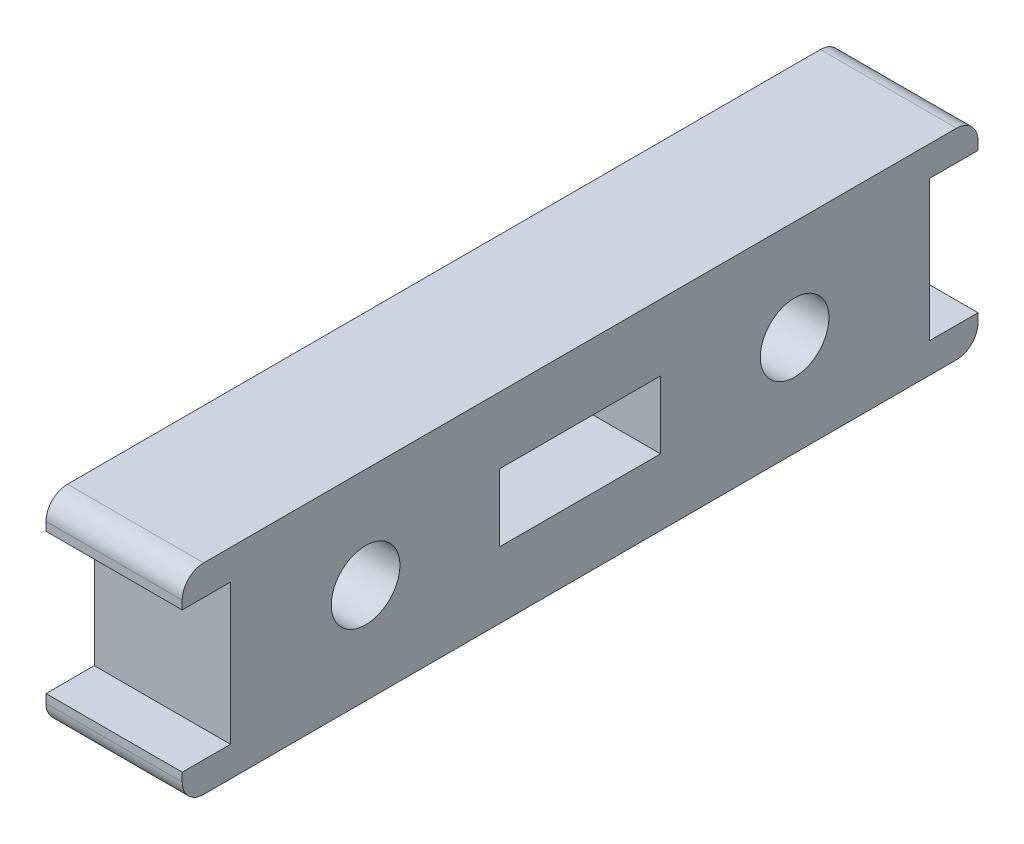
SolidWorks part; units mm, degrees
ref_plane "Front" through (0, 0, 0) normal (0, 0, 1) x (1, 0, 0)
ref_plane "Top" through (0, 0, 0) normal (0, 1, 0) x (1, 0, 0)
ref_plane "Right" through (0, 0, 0) normal (1, 0, 0) x (0, 0, -1)
ref_plane "Plane1" through (6.35, 0, 0) normal (1, 0, 0) x (0, 0, -1)
sketch "Sketch1" plane through (6.35, 0, 0) normal (1, 0, 0) x (0, 0, -1)
  line L0 (37.1, -7.95) -> (34.85, -7.95)
  line L1 (34.85, -7.95) -> (34.85, -1.4)
  line L2 (34.85, -1.4) -> (37.1, -1.4)
  line L3 (37.1, -1.4) -> (37.1, 0)
  line L4 (37.1, 0) -> (0, 0)
  line L5 (0, 0) -> (0, -1.4)
  line L6 (0, -1.4) -> (2.25, -1.4)
  line L7 (2.25, -1.4) -> (2.25, -7.95)
  line L8 (2.25, -7.95) -> (0, -7.95)
  line L9 (0, -7.95) -> (0, -9.35)
  line L10 (0, -9.35) -> (37.1, -9.35)
  line L11 (37.1, -9.35) -> (37.1, -7.95)
extrude "Boss-Extrude1" add sketch "Sketch1" against normal blind 6.35
fillet "Fillet1" radius 1 4 edges at (3.175, 0, -37.1) (3.175, 0, 0) (3.175, -9.35, 0) (3.175, -9.35, -37.1)
sketch "Sketch2" plane through (0, 0, 0) normal (-1, 0, 0) x (0, 0, 1)
  line L0 (-14.8, -3.1) -> (-22.3, -3.1)
  line L1 (-22.3, -3.1) -> (-22.3, -6.25)
  line L2 (-22.3, -6.25) -> (-14.8, -6.25)
  line L3 (-14.8, -6.25) -> (-14.8, -3.1)
extrude "Cut-Extrude1" cut sketch "Sketch2" against normal through all
hole_wizard "Ø3.2 (3.2) Diameter Hole1" positions "Sketch4" profile "Sketch3" hole size "Ø3.2" standard "ANSI Metric"
sketch "Sketch4" plane through (6.35, 0, 0) normal (1, 0, 0) x (0, 0, -1)
  point P0 (28.55, -4.675)
sketch "Sketch3" plane through (6.35, -4.675, -28.55) normal (0, 1, 0) x (0, 0, -1)
  line L0 (0, 0) -> (0, 6.35)
  line L1 (0, 6.35) -> (1.6, 6.35)
  line L2 (1.6, 6.35) -> (1.6, 0)
  line L5 (1.6, 0) -> (0, 0)
  line L11 (0, -6.35) -> (0, 107.95) construction
  dimension "Thru Hole Dia." = 3.2
  dimension "Thru Hole Depth" = 6.35
hole_wizard "Ø3.2 (3.2) Diameter Hole2" positions "Sketch6" profile "Sketch5" hole size "Ø3.2" standard "ANSI Metric"
sketch "Sketch6" plane through (6.35, 0, 0) normal (1, 0, 0) x (0, 0, -1)
  point P0 (8.55, -4.675)
sketch "Sketch5" plane through (6.35, -4.675, -8.55) normal (0, 1, 0) x (0, 0, -1)
  line L0 (0, 0) -> (0, 6.35)
  line L1 (0, 6.35) -> (1.6, 6.35)
  line L2 (1.6, 6.35) -> (1.6, 0)
  line L5 (1.6, 0) -> (0, 0)
  line L11 (0, -6.35) -> (0, 107.95) construction
  dimension "Thru Hole Dia." = 3.2
  dimension "Thru Hole Depth" = 6.35
